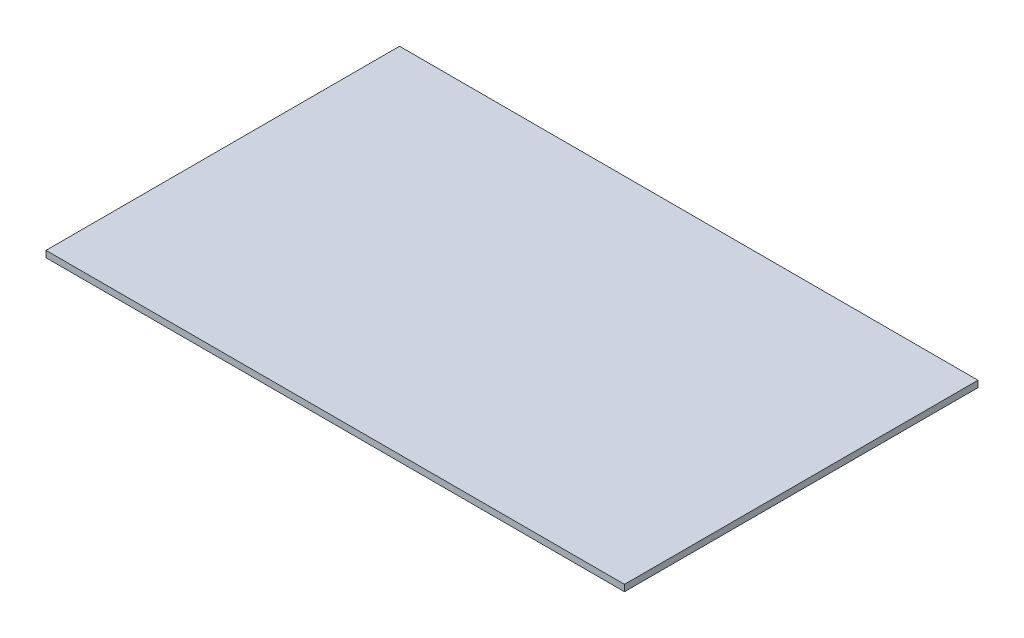
SolidWorks part; units mm, degrees
ref_plane "Front Plane" through (0, 0, 0) normal (0, 0, 1) x (1, 0, 0)
ref_plane "Top Plane" through (0, 0, 0) normal (0, 1, 0) x (1, 0, 0)
ref_plane "Right Plane" through (0, 0, 0) normal (1, 0, 0) x (0, 0, -1)
sketch "Sketch1" plane through (0, 0, 0) normal (0, 1, 0) x (1, 0, 0)
  line L1 (0, 0) -> (90, 0)
  line L2 (0, 0) -> (0, 55)
  line L3 (0, 55) -> (90, 55)
  line L4 (90, 0) -> (90, 55)
  dimension "D1" = 55
  dimension "D2" = 90
extrude "Boss-Extrude1" add sketch "Sketch1" along normal blind 1
